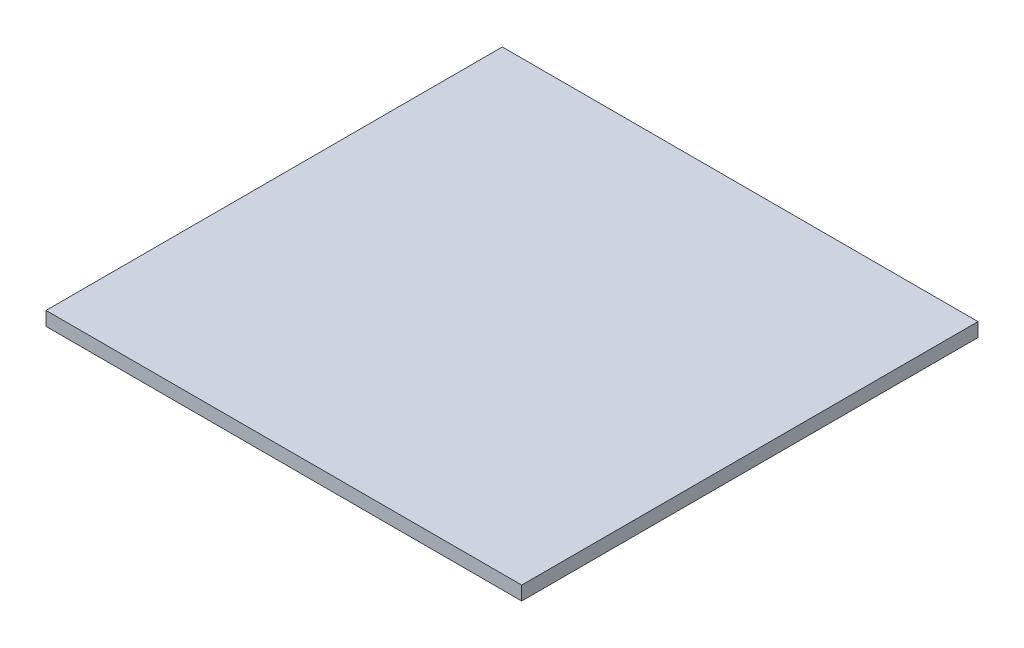
SolidWorks part; units mm, degrees
ref_plane "Front Plane" through (0, 0, 0) normal (0, 0, 1) x (1, 0, 0)
ref_plane "Top Plane" through (0, 0, 0) normal (0, 1, 0) x (1, 0, 0)
ref_plane "Right Plane" through (0, 0, 0) normal (1, 0, 0) x (0, 0, -1)
sketch "Sketch1" plane through (0, 0, 0) normal (0, 1, 0) x (1, 0, 0)
  line L1 (-44.2815, 20.698) -> (58.7185, 20.698)
  line L2 (-44.2815, 20.698) -> (-44.2815, -78.102)
  line L3 (-44.2815, -78.102) -> (58.7185, -78.102)
  line L4 (58.7185, 20.698) -> (58.7185, -78.102)
  dimension "D1" = 103
  dimension "D2" = 98.8
extrude "Boss-Extrude1" add sketch "Sketch1" along normal blind 3
equation "\"Fit\"= 1"
equation "\"cover width\"= 98.8"
equation "\"bottom 5 length\" = 103"
equation "\"thinner acrylic\" = 3"
equation "\"D1@Sketch1\"=\"bottom 5 length\""
equation "\"D2@Sketch1\"=\"cover width\""
equation "\"D1@Boss-Extrude1\"=\"thinner acrylic\""
